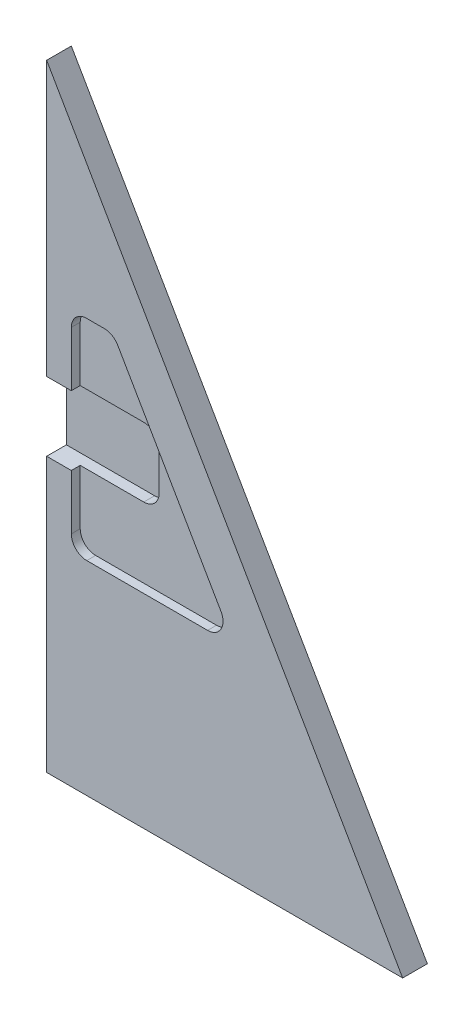
SolidWorks part; units mm, degrees
material "Zoltek Panex 33"
ref_plane "Front Plane" through (0, 0, 0) normal (0, 0, 1) x (1, 0, 0)
ref_plane "Top Plane" through (0, 0, 0) normal (0, 1, 0) x (1, 0, 0)
ref_plane "Right Plane" through (0, 0, 0) normal (1, 0, 0) x (0, 0, -1)
sketch "Sketch1" plane through (0, 0, 0) normal (0, 0, 1) x (1, 0, 0)
  line L0 (0, 63.5) -> (36.6522, 0)
  line L1 (0, 0) -> (36.6522, 0)
  line L2 (0, 0) -> (0, 63.5)
extrude "Extrude1" add sketch "Sketch1" against normal blind 2.54
sketch "Sketch2" plane through (0, 0, 0) normal (-1, 0, 0) x (0, 0, 1)
  line L0 (0, 31.75) -> (-2.54, 31.75) construction
  line L1 (0, 63.5) -> (0, 0) construction
  line L2 (-2.54, 63.5) -> (-2.54, 0) construction
sketch "Sketch4" plane through (0, 0, 0) normal (0, 0, 1) x (1, 0, 0)
  line L0 (0, 31.75) -> (0, 35.306)
  line L1 (0, 63.5) -> (0, 0) construction
  line L2 (0, 31.75) -> (0, 28.194)
  line L3 (0, 35.306) -> (10.668, 35.306)
  line L4 (0, 28.194) -> (10.668, 28.194)
  line L5 (10.668, 35.306) -> (10.668, 28.194)
extrude "Extrude3" cut sketch "Sketch4" against normal blind 2.032
sketch "Sketch3" plane through (0, 0, 0) normal (0, 0, 1) x (1, 0, 0)
  line L0 (0, 31.75) -> (2.54, 31.75) construction
  line L1 (2.54, 31.75) -> (2.54, 42.545)
  line L3 (2.54, 20.955) -> (2.54, 31.75)
  line L4 (2.54, 20.955) -> (19.3197, 20.955)
  line L5 (2.54, 42.545) -> (6.858, 42.545)
  line L6 (19.3197, 20.955) -> (6.858, 42.545)
  line L9 (36.6522, 0) -> (0, 63.5) construction
extrude "Extrude2" cut sketch "Sketch3" against normal blind 0.9144
fillet "Fillet1" radius 1.5875 6 edges at (2.54, 42.545, -0.4572) (10.668, 35.306, -1.4732) (10.668, 28.194, -1.4732) (6.858, 42.545, -0.4572) (19.3197, 20.955, -0.4572) (2.54, 20.955, -0.4572)
